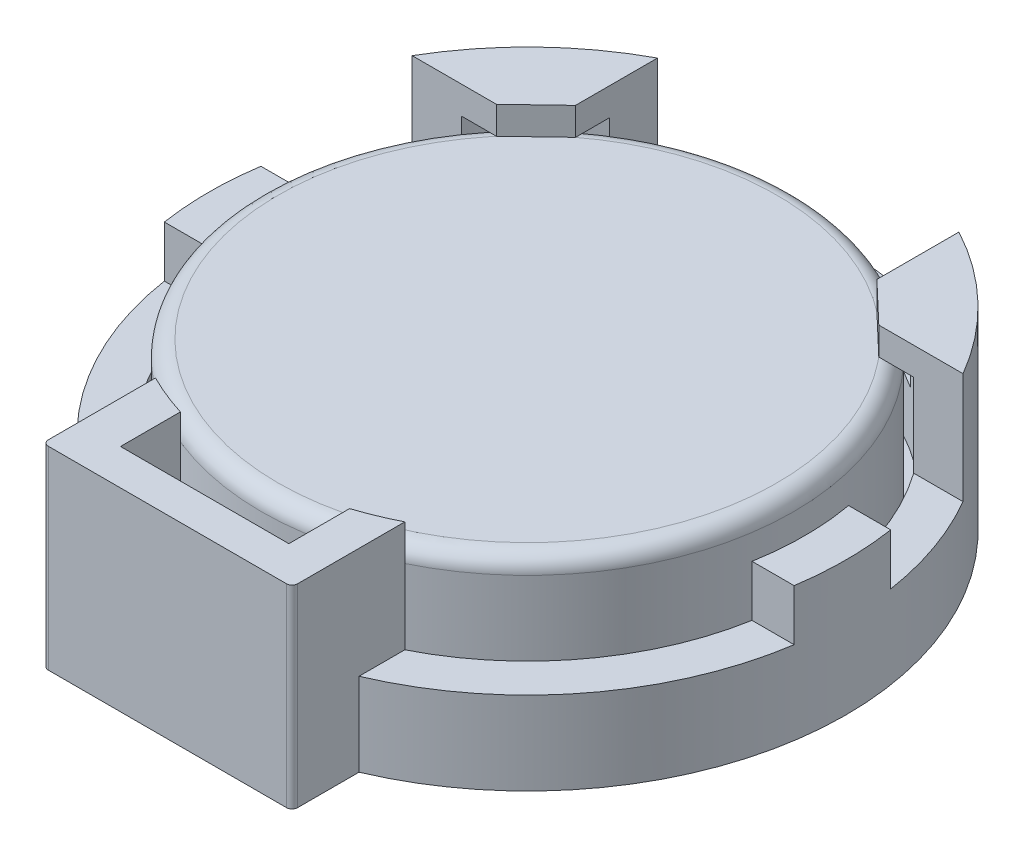
SolidWorks part; units mm, degrees
material "Duranickel(R) 301"
ref_plane "Alzado" through (0, 0, 0) normal (0, 0, 1) x (1, 0, 0)
ref_plane "Planta" through (0, 0, 0) normal (0, 1, 0) x (1, 0, 0)
ref_plane "Vista lateral" through (0, 0, 0) normal (1, 0, 0) x (0, 0, -1)
sketch "Croquis1" plane through (0, 0, 0) normal (0, 1, 0) x (1, 0, 0)
  circle A0 centre (0, 0) radius 11.5
  dimension "D1" = 23
extrude "Extruir1" add sketch "Croquis1" along normal blind 7
sketch "Croquis2" plane through (0, 7, 0) normal (0, 1, 0) x (-1, 0, 0)
  circle A0 centre (0, 0) radius 10
  dimension "D1" = 20
extrude "Cortar-Extruir1" cut sketch "Croquis2" against normal blind 6
sketch "Croquis3" plane through (0, 7, 0) normal (0, 1, 0) x (-1, 0, 0)
  line L0 (0, 0) -> (-13.3981, 0) construction
  line L1 (-12.0533, -1.7432) -> (12.6012, -1.7432)
  line L2 (-12.0533, -1.7432) -> (-12.0533, -5.7781)
  line L3 (-5.4403, -12.651) -> (5.4403, -12.651)
  line L4 (12.6012, -1.7432) -> (12.6012, -5.7781)
  line L5 (12.6012, 1.7432) -> (12.6012, 12.651)
  line L6 (-12.0533, 12.651) -> (12.6012, 12.651)
  line L7 (-12.0533, 1.7432) -> (-12.0533, 12.651)
  line L8 (-12.0533, 1.7432) -> (12.6012, 1.7432)
  line L9 (12.6012, -5.7781) -> (5.4403, -5.7781)
  line L10 (5.4403, -5.7781) -> (5.4403, -12.651)
  line L11 (0, 0) -> (0, 18.6885) construction
  line L12 (-12.0533, -5.7781) -> (-5.4403, -5.7781)
  line L13 (-5.4403, -5.7781) -> (-5.4403, -12.651)
extrude "Cortar-Extruir2" cut sketch "Croquis3" against normal blind 4
sketch "Croquis4" plane through (0, 0, 1.7432) normal (0, 0, 1) x (1, 0, 0)
  line L1 (12.0465, 4.8471) -> (-11.9311, 4.8471)
  line L2 (12.0465, 4.8471) -> (12.0465, 7.6951)
  line L3 (12.0465, 7.6951) -> (-11.9311, 7.6951)
  line L4 (-11.9311, 4.8471) -> (-11.9311, 7.6951)
extrude "Cortar-Extruir3" cut sketch "Croquis4" against normal blind 4
sketch "Croquis5" plane through (0, 3, 0) normal (0, 1, 0) x (-1, 0, 0)
  line L2 (-4.5, 8.9303) -> (-4.5, 13)
  line L3 (-4.5, 13) -> (4.5, 13)
  line L4 (4.5, 8.9303) -> (4.5, 13)
  line L6 (-3.088, 9.5113) -> (-3.088, 11.7047)
  line L7 (-3.088, 11.7047) -> (2.9884, 11.7047)
  line L8 (2.9884, 9.543) -> (2.9884, 11.7047)
  arc A0 (-4.5, 8.9303) -> (-3.088, 9.5113) centre (0, 0) cw
  circle A1 centre (0, 0) radius 10 construction
  arc A2 (2.9884, 9.543) -> (4.5, 8.9303) centre (0, 0) cw
  dimension "D1" = 9
  dimension "D2" = 4.5
  dimension "D3" = 13
extrude "Extruir2" add sketch "Croquis5" along normal blind 4 and the other way blind 3
fillet "Redondeo1" radius 0.2 2 edges at (4.5, 3.5, 13) (-4.5, 3.5, 13)
sketch "Croquis6" plane through (0, 1, 0) normal (0, 1, 0) x (-1, 0, 0)
  circle A0 centre (0, 0) radius 9.6011
extrude "Extruir3" add sketch "Croquis6" along normal blind 5 separate body
fillet "Redondeo2" radius 0.6 1 edges at (0, 6, 9.6011)
sketch "Croquis7" plane through (0, 7, 0) normal (0, 1, 0) x (-1, 0, 0)
  line L0 (-5.4403, -8.3907) -> (-5.4403, -7.171)
  line L1 (-8.1617, -5.7781) -> (-6.9017, -5.7781)
  line L2 (-6.9017, -5.7781) -> (-5.4403, -7.171)
  line L3 (0, 0) -> (0, -13.6373) construction
  line L4 (6.9017, -5.7781) -> (5.4403, -7.171)
  line L5 (8.1617, -5.7781) -> (6.9017, -5.7781)
  line L6 (5.4403, -8.3907) -> (5.4403, -7.171)
  circle A0 centre (0, 0) radius 9.0011 construction
  arc A1 (-8.1617, -5.7781) -> (-5.4403, -8.3907) centre (0, 0) ccw
  arc A2 (8.1617, -5.7781) -> (5.4403, -8.3907) centre (0, 0) cw
extrude "Extruir5" add sketch "Croquis7" against normal blind 1 separate body
combine bodies "Combinar1" operation type add bodies to combine 105 109 108
